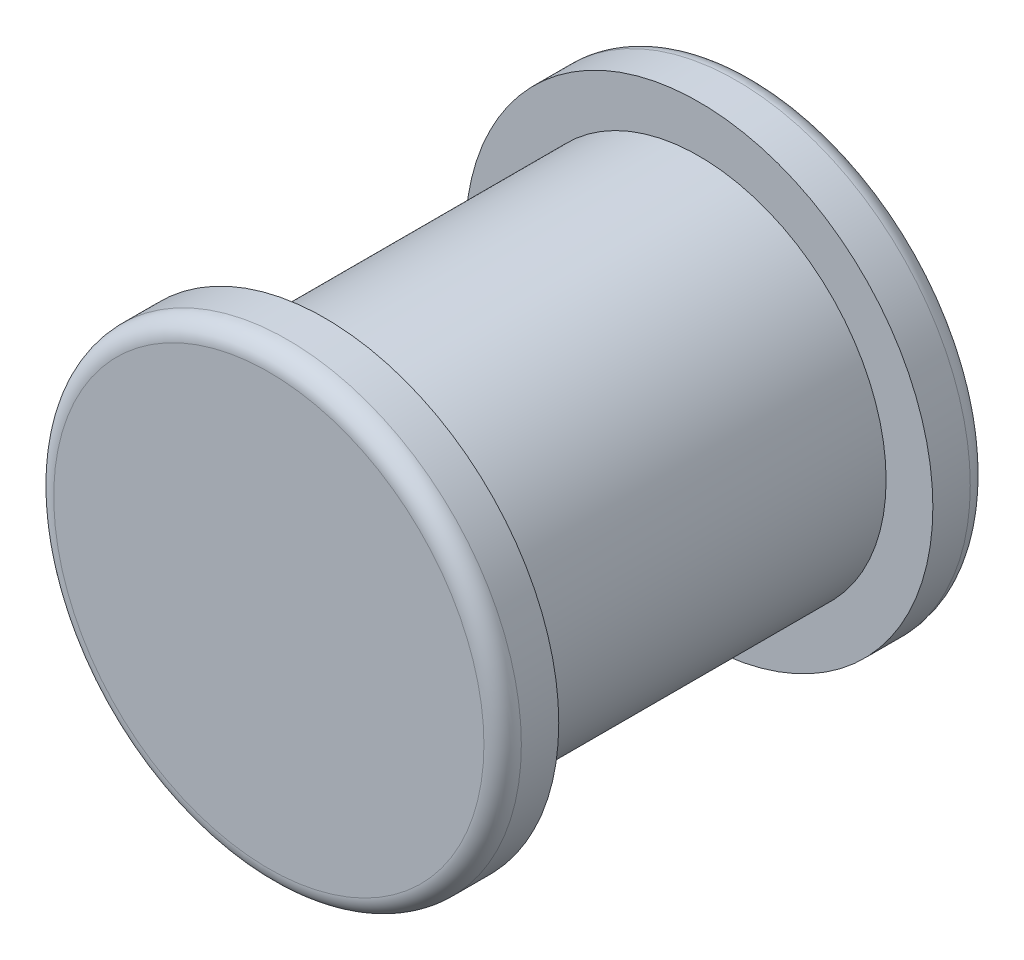
SolidWorks part; units mm, degrees
ref_plane "Front Plane" through (0, 0, 0) normal (0, 0, 1) x (1, 0, 0)
ref_plane "Top Plane" through (0, 0, 0) normal (0, 1, 0) x (1, 0, 0)
ref_plane "Right Plane" through (0, 0, 0) normal (1, 0, 0) x (0, 0, -1)
sketch "Sketch1" plane through (0, 0, 0) normal (0, 0, 1) x (1, 0, 0)
  circle A0 centre (0, 0) radius 10
  dimension "D1" = 20
extrude "Boss-Extrude1" add sketch "Sketch1" along normal blind 20
sketch "Sketch2" plane through (0, 0, 0) normal (0, 0, -1) x (-1, 0, 0)
  circle A0 centre (0, 0) radius 12.5
  dimension "D1" = 25
extrude "Boss-Extrude2" add sketch "Sketch2" along normal blind 3
fillet "Fillet1" radius 1 1 edges at (-12.5, 0, -3)
ref_plane "Plane1" through (0, 0, 10) normal (0, 0, 1) x (1, 0, 0)
mirror "Mirror1" about plane through (0, 0, 10) normal (0, 0, 1) of "Fillet1", "Boss-Extrude2"
